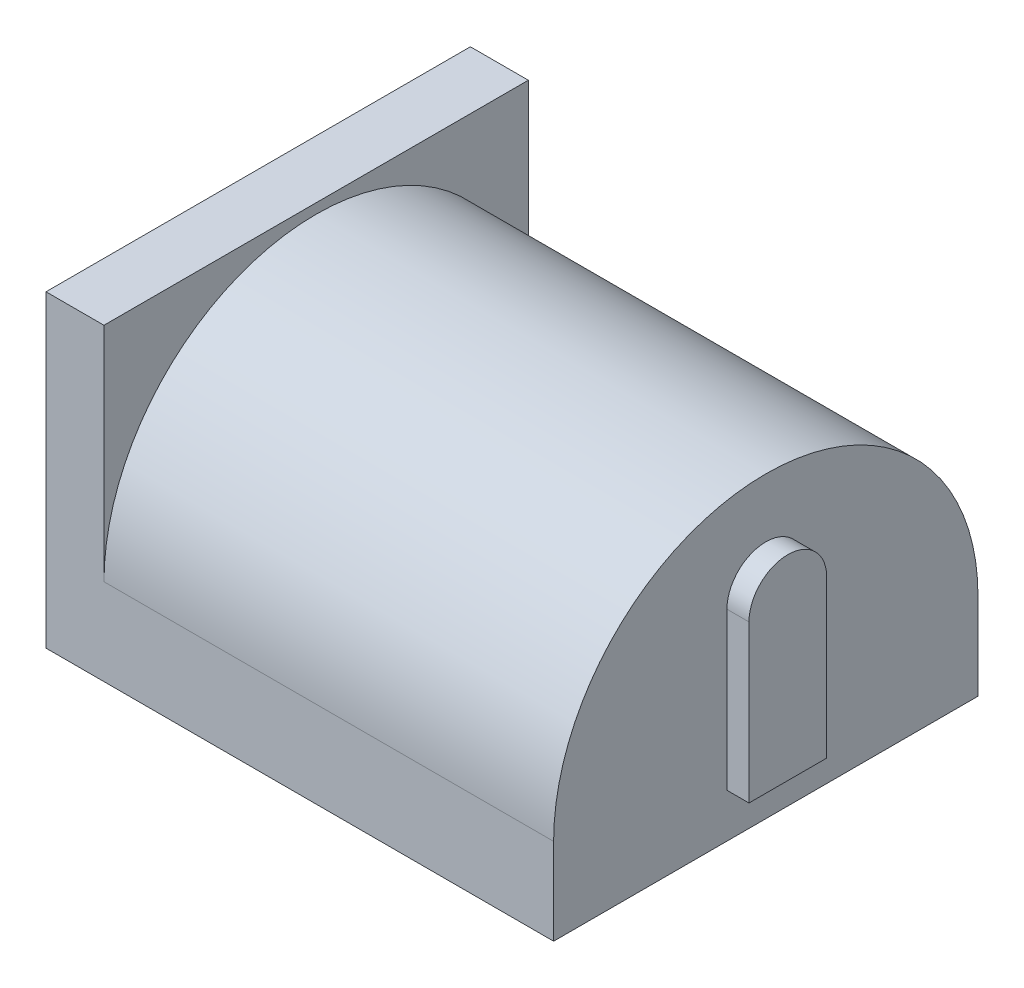
SolidWorks part; units mm, degrees
material "NEOPRENO"
ref_plane "Alzado" through (0, 0, 0) normal (0, 0, 1) x (1, 0, 0)
ref_plane "Planta" through (0, 0, 0) normal (0, 1, 0) x (1, 0, 0)
ref_plane "Vista lateral" through (0, 0, 0) normal (1, 0, 0) x (0, 0, -1)
sketch "Croquis1" plane through (0, 31.4682, 0) normal (0, 1, 0) x (1, 0, 0)
  line L0 (-14.2075, -74.0387) -> (-2.6948, -74.0387) construction
  line L1 (-14.2075, -64.4139) -> (-12.893, -64.4139)
  line L2 (-14.2075, -64.4139) -> (-14.2075, -74.0387)
  line L3 (-14.2075, -74.0387) -> (-12.893, -74.0387)
  line L4 (-12.893, -64.4139) -> (-12.893, -74.0387)
extrude "Saliente-Extruir1" add sketch "Croquis1" along normal blind 7
sketch "Croquis2" plane through (-12.893, 0, 0) normal (1, 0, 0) x (0, 0, -1)
  line L0 (-64.4139, 38.4682) -> (-64.4139, 31.4682) construction
  line L1 (-74.0387, 38.4682) -> (-74.0387, 31.4682) construction
  line L2 (-64.4139, 33.4301) -> (-64.4139, 31.4682)
  line L3 (-64.4139, 31.4682) -> (-74.0387, 31.4682)
  line L4 (-74.0387, 31.4682) -> (-74.0387, 33.4301)
  arc A0 (-64.8319, 31.4682) -> (-73.6206, 31.4682) centre (-69.2263, 33.4301) ccw
  line M1 (-74.0387, 31.4682) -> (-64.4139, 31.4682)
  line M2 (-64.4139, 31.4682) -> (-64.4139, 38.4682)
  line M4 (-74.0387, 38.4682) -> (-74.0387, 31.4682)
extrude "Saliente-Extruir2" add sketch "Croquis2" along normal up to vertex (10.1982 mm away) contours A0 M4 M1 | A0 M1 M2 | A0 L3
sketch "Croquis3" plane through (-14.2075, 0, 0) normal (-1, 0, 0) x (0, 0, 1)
  arc A0 (74.0387, 33.4301) -> (64.4139, 33.4301) centre (69.2263, 33.4301) ccw construction
  arc A1 (74.0387, 33.4301) -> (64.4139, 33.4301) centre (69.2263, 33.4301) ccw
  circle A2 centre (69.2263, 35.2668) radius 2.2161
extrude "Cortar-Extruir1" cut sketch "Croquis3" against normal blind 10 contours A2
sketch "Croquis4" plane through (-4.2075, 0, 0) normal (-1, 0, 0) x (0, 0, 1)
  circle A0 centre (69.2263, 35.2668) radius 0.4915
extrude "Saliente-Extruir3" add sketch "Croquis4" along normal blind 8
fillet "Redondeo1" radius 0.2 1 edges at (-12.2075, 35.2668, 69.7178)
sketch "Croquis5" plane through (-2.6948, 0, 0) normal (1, 0, 0) x (0, 0, -1)
  line L0 (-70.1081, 36.0248) -> (-70.1081, 32.4682)
  line L1 (-72.9707, 32.4682) -> (-69.7906, 32.4682) construction
  line L2 (-70.1081, 32.4682) -> (-68.3445, 32.4682)
  line L3 (-69.7906, 32.4682) -> (-39.174, 32.4682) construction
  line L4 (-68.3445, 32.4682) -> (-68.3445, 36.0248)
  arc A0 (-68.3445, 36.0248) -> (-70.1081, 36.0248) centre (-69.2263, 36.0248) ccw
extrude "Saliente-Extruir4" add sketch "Croquis5" along normal blind 0.5
